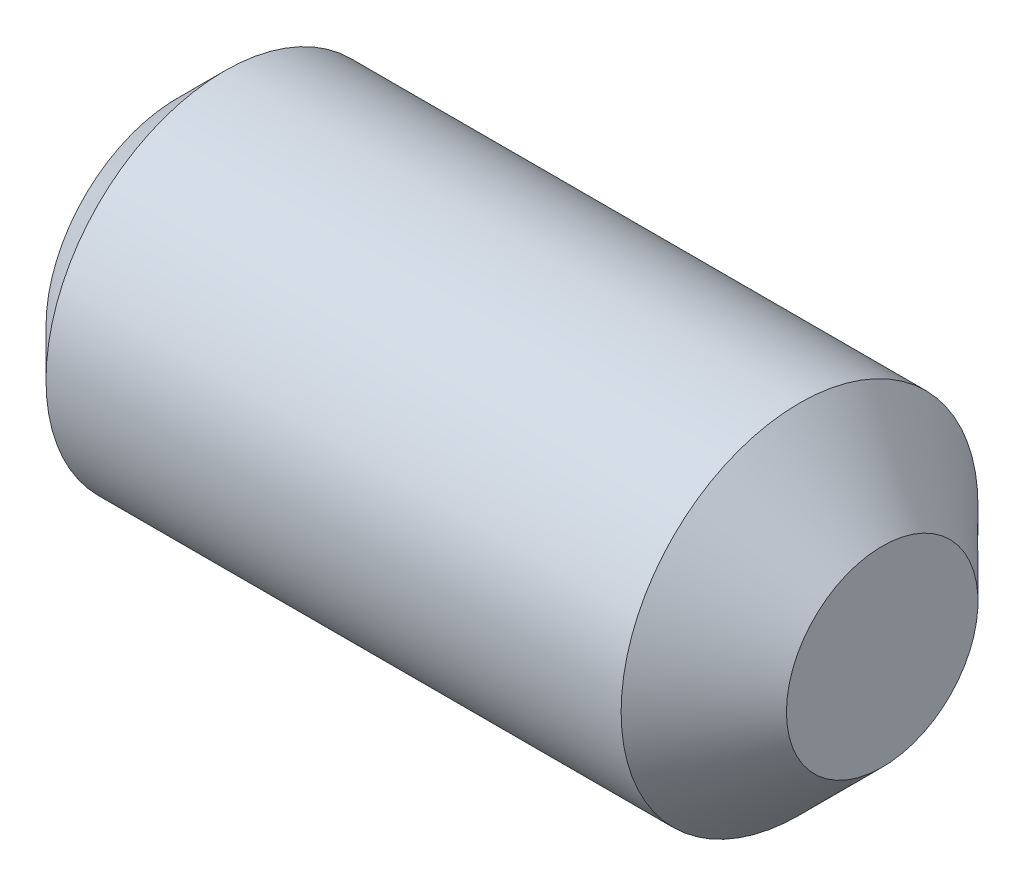
SolidWorks part; units mm, degrees
revolve "BaseBody" add sketch "BodySke" angle 360 about L5
sketch "BodySke" plane through (0, 0, 0) normal (0, 0, 1) x (1, 0, 0)
  line L0 (0, 0) -> (0, 1.7831)
  line L1 (0, 1.7831) -> (0.6299, 2.413)
  line L2 (0.6299, 2.413) -> (8.4074, 2.413)
  line L3 (8.4074, 2.413) -> (9.525, 1.2954)
  line L4 (9.525, 0) -> (0, 0)
  line L5 (-12.7, 0) -> (88.9, 0) construction
  line L6 (9.525, 1.2954) -> (9.525, 0)
  line L7 (9.525, 1.2954) -> (9.525, 10.8204) construction
  line L8 (0, -1.7831) -> (0.6299, -2.413) construction
  line L9 (1.0592, 15.875) -> (1.0592, -3.175) construction
  line L10 (8.4074, -2.413) -> (9.525, -1.2954) construction
  dimension "Diameter" = 4.826
  dimension "Drive_ch_ang" = 45
  dimension "Minor_dia" = 3.5662
  dimension "Cup_nose_ang" = 45
  dimension "Cup_dia" = 2.5908
  dimension "Length" = 9.525
  dimension "Advance" = 1.0592
cosmetic thread "ThreadCosmetic" [suppressed] parameters "Thread_minor"=3.5662
ref_plane "Plane1" through (0, 0, 0) normal (0, 0, 1) x (1, 0, 0)
ref_plane "Plane2" through (0, 0, 0) normal (0, 1, 0) x (1, 0, 0)
ref_plane "Plane3" through (0, 0, 0) normal (1, 0, 0) x (0, 0, -1)
other "Configuration Table"
sketch "Sketch2" plane through (0, 0, 0) normal (-1, 0, 0) x (0, 0, 1)
  line L0 (0.687, 1.19) -> (-0.687, 1.19)
  line L1 (-0.687, 1.19) -> (-1.3741, 0)
  line L2 (0.687, 1.19) -> (1.3741, 0)
  line L3 (0.687, -1.19) -> (1.3741, 0)
  line L4 (0.687, -1.19) -> (-0.687, -1.19)
  line L5 (-0.687, -1.19) -> (-1.3741, 0)
  dimension "Hex_size" = 2.38
  dimension "D2" = 1.19
  dimension "D3" = 1.19
extrude "Hex" cut sketch "Sketch2" against normal blind 2.54
sketch "Sketch4" plane through (0, 4.7709, -0.5249) normal (-1, 0, 0) x (0, 0, 1)
  line L0 (0.5249, -4.7709) -> (1.9854, -4.7709)
  line L1 (0.5249, -4.7709) -> (6.6732, -1.2211) construction
  line L2 (0.5249, -4.7709) -> (1.2551, -3.506)
  line L3 (1.7258, -4.4441) -> (1.9182, -4.333)
  line L4 (1.4083, -3.8942) -> (1.6007, -3.7831)
  arc A0 (1.7258, -4.4441) -> (1.4083, -3.8942) centre (0.5249, -4.7709) ccw
  arc A1 (1.9854, -4.7709) -> (1.9182, -4.333) centre (0.5249, -4.7709) ccw
  arc A2 (1.2551, -3.506) -> (1.6007, -3.7831) centre (0.5249, -4.7709) cw
  circle A3 centre (0.5249, -4.7709) radius 1.2446 construction
  circle A4 centre (0.5249, -4.7709) radius 1.4605 construction
  dimension "Spline_n_dim" = 2.4892
  dimension "Spline_m_dim" = 2.921
  dimension "D1" = 30
  dimension "Spline_a_dim" = 60
  dimension "Spline_p_dim" = 0.635
  dimension "D3" = 0.3175
extrude "Spline" [suppressed] cut sketch "Sketch4" against normal blind 2.032
pattern_circular "CirPattern1" [suppressed] count 6 every 60 about axis through (-12.7, 0, 0) along (1, 0, 0)
sketch "ThdSchSke" plane through (0, 0, 0) normal (0, 0, 1) x (1, 0, 0)
  line L0 (0.6299, -1.7831) -> (0.1888, -2.413)
  line L1 (0.6299, -1.7831) -> (1.071, -2.413)
  line L2 (1.071, -2.413) -> (1.071, -3.0162)
  line L3 (-3.175, 0) -> (5.1513, 0) construction
  line L4 (0.6299, 2.413) -> (0.6299, -2.413) construction
  line L5 (1.071, -3.0162) -> (0.1888, -3.0162)
  line L6 (0.1888, -3.0162) -> (0.1888, -2.413)
  dimension "Thread_minor" = 3.5662
  dimension "Diameter" = 4.826
revolve "ThreadSchematic" [suppressed] cut sketch "ThdSchSke" angle 360 about L3
pattern_linear "ThdSchPat" [suppressed]
equation "\"D2@Sketch2\" = \"Hex_size@Sketch2\" / 2"
equation "\"D3@Sketch2\" = \"Hex_size@Sketch2\" / 2"
equation "\"Thread_minor@ThreadCosmetic\" = \"Minor_dia@BodySke\""
equation "\"D1@Sketch4\" = \"Spline_a_dim@Sketch4\" / 2"
equation "\"D3@Sketch4\" = \"Spline_p_dim@Sketch4\" / 2"
equation "\"D2@CirPattern1\" = \"Spline_a_dim@Sketch4\""
equation "\"Num_teeth@CirPattern1\" = 360 / \"D2@CirPattern1\""
equation "\"Thread_minor@ThdSchSke\" = \"Thread_minor@ThreadCosmetic\""
equation "\"Diameter@ThdSchSke\" = \"Diameter@BodySke\""
equation "\"Overcut@ThdSchSke\" = \"Diameter@BodySke\" * 1.25"
equation "\"Num_threads@ThdSchPat\" = int( (\"Length@BodySke\" - ( ( ( \"Diameter@BodySke\" - \"Minor_dia@BodySke\" ) * 0.5 ) / tan( \"Drive_ch_ang@BodySke\" * 0.017453292 ) ) - ( ( ( \"Diameter@BodySke\" - \"Cup_dia@BodySke\" ) * 0.5 ) * tan( \"Cup_nose_ang@BodySke\" * 0.017453292 ) ) ) / \"Advance@BodySke\" + 0.999 )  + 1"
equation "\"Advance@ThdSchPat\" = (\"Length@BodySke\" - ( ( ( \"Diameter@BodySke\" - \"Minor_dia@BodySke\" ) * 0.5 ) / tan( \"Drive_ch_ang@BodySke\" * 0.017453292 ) ) - ( ( ( \"Diameter@BodySke\" - \"Cup_dia@BodySke\" ) * 0.5 ) * tan( \"Cup_nose_ang@BodySke\" * 0.017453292 ) ) ) /  (\"Num_threads@ThdSchPat\" - 1) 'relax it"
equation "' \"Num_threads@ThdSchPat\" = \"Num_threads@ThdSchPat\" - sgn( \"Num_threads@ThdSchPat\" - 1) '---chamfered tips only---"
